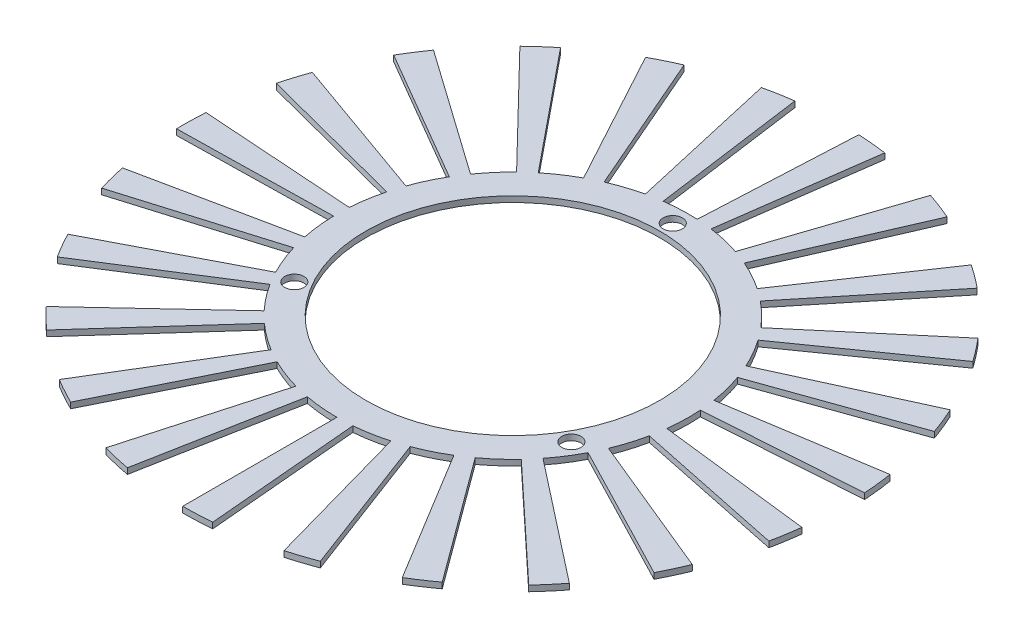
SolidWorks part; units mm, degrees
material "AISI 1010 Steel, hot rolled bar"
ref_plane "Front Plane" through (0, 0, 0) normal (0, 0, 1) x (1, 0, 0)
ref_plane "Top Plane" through (0, 0, 0) normal (0, 1, 0) x (1, 0, 0)
ref_plane "Right Plane" through (0, 0, 0) normal (1, 0, 0) x (0, 0, -1)
sketch "Sketch1" plane through (0, 0, 0) normal (0, 1, 0) x (1, 0, 0)
  circle A0 centre (0, 0) radius 25.25
  dimension "D1" = 50.5
extrude "Extrude-Thin1" add sketch "Sketch1" against normal blind 1 thin
sketch "Sketch2" plane through (0, 0, 0) normal (0, 1, 0) x (1, 0, 0)
  line L0 (0, -30.25) -> (0, 30.25) construction
  line L1 (0, 0) -> (23.8157, -13.75) construction
  line L2 (0, 0) -> (-23.8157, -13.75) construction
  circle A0 centre (0, 27.5) radius 1.65
  circle A1 centre (0, 0) radius 30.25 construction
  circle A4 centre (0, 0) radius 27.5 construction
  circle A7 centre (23.8157, -13.75) radius 1.65
  circle A8 centre (-23.8157, -13.75) radius 1.65
  dimension "D1" = 55
  dimension "D2" = 3.3
  dimension "D3" = 120
  dimension "D4" = 120
extrude "Cut-Extrude3" cut sketch "Sketch2" against normal blind 10
sketch "Sketch5" plane through (0, -1, 0) normal (0, -1, 0) x (1, 0, 0)
  line L0 (0, 0) -> (0, 35.9971) construction
  line L1 (0, 0) -> (2.9726, 33.977) construction
  line L2 (0, 56.75) -> (0, 30.25)
  line L3 (2.6365, 30.1349) -> (4.9461, 56.534)
  line L4 (15.311, 54.6456) -> (8.1614, 29.1282)
  line L5 (10.669, 28.3061) -> (20.0154, 53.1032)
  line L6 (29.4864, 48.4883) -> (15.7174, 25.8462)
  line L7 (17.9102, 24.378) -> (33.6002, 45.7339)
  line L8 (41.4749, 38.7349) -> (22.1078, 20.6472)
  line L9 (23.8232, 18.6418) -> (44.6931, 34.9727)
  line L10 (50.3875, 26.1087) -> (26.8585, 13.917)
  line L11 (27.9693, 11.5231) -> (52.4713, 21.6178)
  line L12 (55.563, 11.5461) -> (29.6173, 6.1545)
  line L13 (30.041, 3.5498) -> (56.3579, 6.6596)
  line L14 (56.6177, -3.8728) -> (30.1795, -2.0643)
  line L15 (29.8847, -4.6868) -> (56.0647, -8.7926)
  line L16 (53.4733, -19.0044) -> (28.5034, -10.1301)
  line L17 (27.512, -12.5758) -> (51.6135, -23.5926)
  line L18 (46.363, -32.7266) -> (24.7133, -17.4446)
  line L19 (23.0989, -19.5321) -> (43.3343, -36.6429)
  line L20 (35.8142, -44.0216) -> (19.0904, -23.4653)
  line L21 (16.9726, -25.0398) -> (31.8412, -46.9755)
  line L22 (22.6093, -52.0517) -> (12.0516, -27.7456)
  line L23 (9.5876, -28.6904) -> (17.9866, -53.8242)
  line L24 (7.7275, -56.2214) -> (4.119, -29.9682)
  line L25 (1.4915, -30.2132) -> (2.798, -56.681)
  line L26 (-7.7275, -56.2214) -> (-4.119, -29.9682)
  line L27 (-6.7153, -29.4952) -> (-12.5981, -55.334)
  line L28 (-22.6093, -52.0517) -> (-12.0516, -27.7456)
  line L29 (-14.424, -26.5897) -> (-27.0598, -49.8831)
  line L30 (-35.8142, -44.0216) -> (-19.0904, -23.4653)
  line L31 (-21.0629, -21.7121) -> (-39.5147, -40.7327)
  line L32 (-46.363, -32.7266) -> (-24.7133, -17.4446)
  line L33 (-26.1397, -15.2243) -> (-49.0389, -28.5613)
  line L34 (-53.4733, -19.0044) -> (-28.5034, -10.1301)
  line L35 (-29.2778, -7.6073) -> (-54.9262, -14.2716)
  line L36 (-56.6177, -3.8728) -> (-30.1795, -2.0643)
  line L37 (-30.2446, 0.5738) -> (-56.7398, 1.0765)
  line L38 (-55.563, 11.5461) -> (-29.6173, 6.1545)
  line L39 (-28.9682, 8.7124) -> (-54.3453, 16.3448)
  line L40 (-50.3875, 26.1087) -> (-26.8585, 13.917)
  line L41 (-25.5434, 16.2049) -> (-47.9202, 30.4009)
  line L42 (-41.4749, 38.7349) -> (-22.1078, 20.6472)
  line L43 (-20.2241, 22.4955) -> (-37.9411, 42.2023)
  line L44 (-29.4864, 48.4883) -> (-15.7174, 25.8462)
  line L45 (-13.405, 27.1177) -> (-25.1482, 50.8737)
  line L46 (-15.311, 54.6456) -> (-8.1614, 29.1282)
  line L47 (-5.5916, 29.7287) -> (-10.49, 55.7721)
  circle A0 centre (0, 0) radius 30.25 construction
  arc A1 (2.6365, 30.1349) -> (0, 30.25) centre (0, 0) ccw
  arc A2 (4.9461, 56.534) -> (0, 56.75) centre (0, 0) ccw
  arc A3 (20.0154, 53.1032) -> (15.311, 54.6456) centre (0, 0) ccw
  arc A4 (10.669, 28.3061) -> (8.1614, 29.1282) centre (0, 0) ccw
  arc A5 (33.6002, 45.7339) -> (29.4864, 48.4883) centre (0, 0) ccw
  arc A6 (17.9102, 24.378) -> (15.7174, 25.8462) centre (0, 0) ccw
  arc A7 (44.6931, 34.9727) -> (41.4749, 38.7349) centre (0, 0) ccw
  arc A8 (23.8232, 18.6418) -> (22.1078, 20.6472) centre (0, 0) ccw
  arc A9 (52.4713, 21.6178) -> (50.3875, 26.1087) centre (0, 0) ccw
  arc A10 (27.9693, 11.5231) -> (26.8585, 13.917) centre (0, 0) ccw
  arc A11 (56.3579, 6.6596) -> (55.563, 11.5461) centre (0, 0) ccw
  arc A12 (30.041, 3.5498) -> (29.6173, 6.1545) centre (0, 0) ccw
  arc A13 (56.0647, -8.7926) -> (56.6177, -3.8728) centre (0, 0) ccw
  arc A14 (29.8847, -4.6868) -> (30.1795, -2.0643) centre (0, 0) ccw
  arc A15 (51.6135, -23.5926) -> (53.4733, -19.0044) centre (0, 0) ccw
  arc A16 (27.512, -12.5758) -> (28.5034, -10.1301) centre (0, 0) ccw
  arc A17 (43.3343, -36.6429) -> (46.363, -32.7266) centre (0, 0) ccw
  arc A18 (23.0989, -19.5321) -> (24.7133, -17.4446) centre (0, 0) ccw
  arc A19 (31.8412, -46.9755) -> (35.8142, -44.0216) centre (0, 0) ccw
  arc A20 (16.9726, -25.0398) -> (19.0904, -23.4653) centre (0, 0) ccw
  arc A21 (17.9866, -53.8242) -> (22.6093, -52.0517) centre (0, 0) ccw
  arc A22 (9.5876, -28.6904) -> (12.0516, -27.7456) centre (0, 0) ccw
  arc A23 (2.798, -56.681) -> (7.7275, -56.2214) centre (0, 0) ccw
  arc A24 (1.4915, -30.2132) -> (4.119, -29.9682) centre (0, 0) ccw
  arc A25 (-12.5981, -55.334) -> (-7.7275, -56.2214) centre (0, 0) ccw
  arc A26 (-6.7153, -29.4952) -> (-4.119, -29.9682) centre (0, 0) ccw
  arc A27 (-27.0598, -49.8831) -> (-22.6093, -52.0517) centre (0, 0) ccw
  arc A28 (-14.424, -26.5897) -> (-12.0516, -27.7456) centre (0, 0) ccw
  arc A29 (-39.5147, -40.7327) -> (-35.8142, -44.0216) centre (0, 0) ccw
  arc A30 (-21.0629, -21.7121) -> (-19.0904, -23.4653) centre (0, 0) ccw
  arc A31 (-49.0389, -28.5613) -> (-46.363, -32.7266) centre (0, 0) ccw
  arc A32 (-26.1397, -15.2243) -> (-24.7133, -17.4446) centre (0, 0) ccw
  arc A33 (-54.9262, -14.2716) -> (-53.4733, -19.0044) centre (0, 0) ccw
  arc A34 (-29.2778, -7.6073) -> (-28.5034, -10.1301) centre (0, 0) ccw
  arc A35 (-56.7398, 1.0765) -> (-56.6177, -3.8728) centre (0, 0) ccw
  arc A36 (-30.2446, 0.5738) -> (-30.1795, -2.0643) centre (0, 0) ccw
  arc A37 (-54.3453, 16.3448) -> (-55.563, 11.5461) centre (0, 0) ccw
  arc A38 (-28.9682, 8.7124) -> (-29.6173, 6.1545) centre (0, 0) ccw
  arc A39 (-47.9202, 30.4009) -> (-50.3875, 26.1087) centre (0, 0) ccw
  arc A40 (-25.5434, 16.2049) -> (-26.8585, 13.917) centre (0, 0) ccw
  arc A41 (-37.9411, 42.2023) -> (-41.4749, 38.7349) centre (0, 0) ccw
  arc A42 (-20.2241, 22.4955) -> (-22.1078, 20.6472) centre (0, 0) ccw
  arc A43 (-25.1482, 50.8737) -> (-29.4864, 48.4883) centre (0, 0) ccw
  arc A44 (-13.405, 27.1177) -> (-15.7174, 25.8462) centre (0, 0) ccw
  arc A45 (-10.49, 55.7721) -> (-15.311, 54.6456) centre (0, 0) ccw
  arc A46 (-5.5916, 29.7287) -> (-8.1614, 29.1282) centre (0, 0) ccw
  point P87 (0, 0)
  dimension "D2" = 26.5
  dimension "D1" = 5
  dimension "D3" = 23
extrude "Boss-Extrude1" add sketch "Sketch5" against normal blind 1
